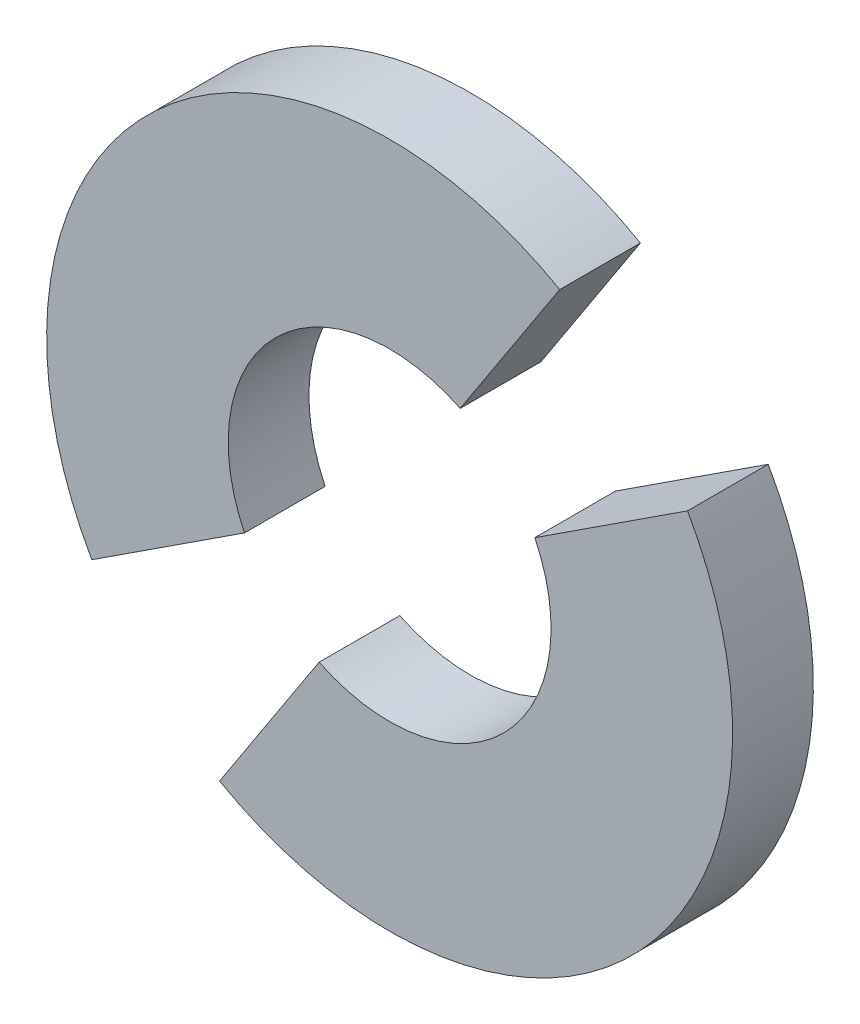
SolidWorks part; units mm, degrees
ref_plane "Front Plane" through (0, 0, 0) normal (0, 0, 1) x (1, 0, 0)
ref_plane "Top Plane" through (0, 0, 0) normal (0, 1, 0) x (1, 0, 0)
ref_plane "Right Plane" through (0, 0, 0) normal (1, 0, 0) x (0, 0, -1)
sketch "Sketch1" plane through (0, 0, 0) normal (0, 0, 1) x (1, 0, 0)
  circle A0 centre (0, 0) radius 31.75 construction
  dimension "D1" = 63.5
sketch "Sketch2" plane through (0, 0, 0) normal (0, 0, 1) x (1, 0, 0)
  line L0 (-10.5566, -20.3813) -> (-18.3879, -32.3945) construction
  line L1 (18.4303, 4.4238) -> (6.4171, -3.4075) construction
  line L2 (-28.4411, -22.3413) -> (-16.4279, -14.51) construction
  line L3 (0.5458, 2.4638) -> (8.3771, 14.477) construction
  line L4 (-10.5566, -20.3813) -> (-18.3879, -32.3945)
  line L5 (18.4303, 4.4238) -> (6.4171, -3.4075)
  line L6 (-28.4411, -22.3413) -> (-16.4279, -14.51)
  line L7 (0.5458, 2.4638) -> (8.3771, 14.477)
  arc A0 (-10.5566, -20.3813) -> (6.4171, -3.4075) centre (-5.0054, -8.9588) ccw construction
  arc A1 (-18.3879, -32.3945) -> (18.4303, 4.4238) centre (-5.0054, -8.9588) ccw construction
  arc A2 (0.5458, 2.4638) -> (-16.4279, -14.51) centre (-5.0054, -8.9588) ccw construction
  arc A3 (8.3771, 14.477) -> (-28.4411, -22.3413) centre (-5.0054, -8.9588) ccw construction
  arc A4 (-10.5566, -20.3813) -> (6.4171, -3.4075) centre (-5.0054, -8.9588) ccw
  arc A5 (-18.3879, -32.3945) -> (18.4303, 4.4238) centre (-5.0054, -8.9588) ccw
  arc A6 (0.5458, 2.4638) -> (-16.4279, -14.51) centre (-5.0054, -8.9588) ccw
  arc A7 (8.3771, 14.477) -> (-28.4411, -22.3413) centre (-5.0054, -8.9588) ccw
extrude "Boss-Extrude2" add sketch "Sketch2" along normal blind 6.35
